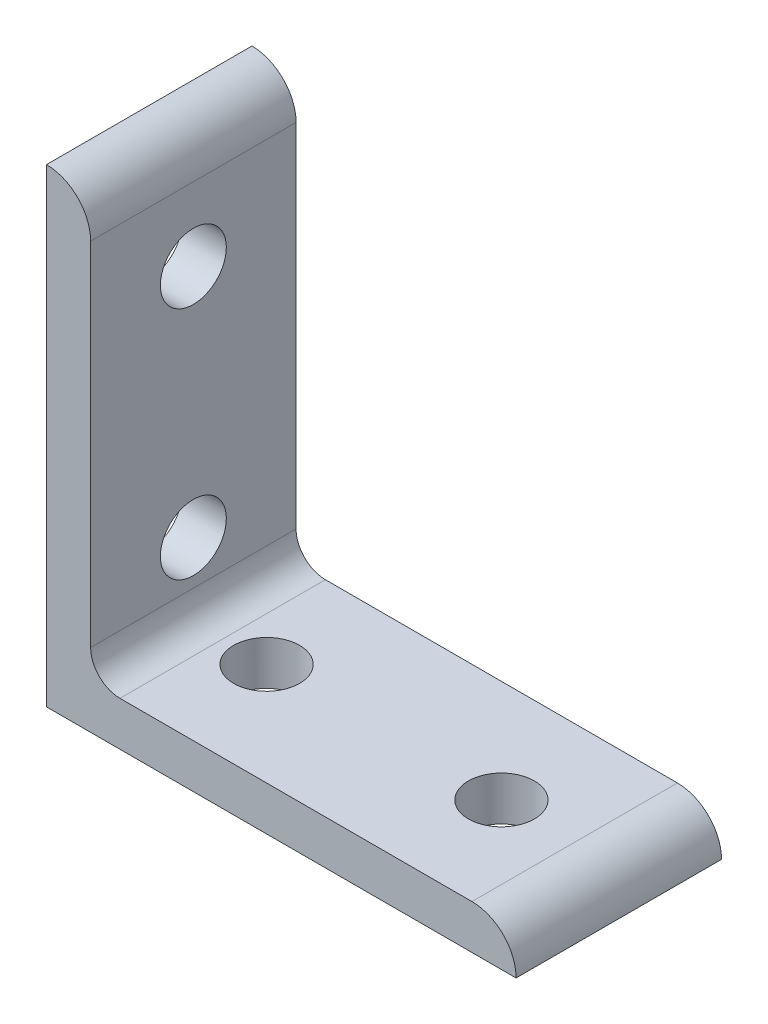
SolidWorks part; units mm, degrees
ref_plane "Front Plane" through (0, 0, 0) normal (0, 0, 1) x (1, 0, 0)
ref_plane "Top Plane" through (0, 0, 0) normal (0, 1, 0) x (1, 0, 0)
ref_plane "Right Plane" through (0, 0, 0) normal (1, 0, 0) x (0, 0, -1)
sketch "Sketch1" plane through (0, 0, 0) normal (0, 0, 1) x (1, 0, 0)
  line L0 (0, 0) -> (0, 50.8)
  line L1 (4.7752, 46.0248) -> (4.7752, 50.8) construction
  line L2 (4.7752, 46.0248) -> (4.7752, 7.9502)
  line L3 (7.9502, 4.7752) -> (46.0248, 4.7752)
  line L4 (4.7752, 50.8) -> (0, 50.8) construction
  line L5 (50.8, 0) -> (0, 0)
  line L6 (46.0248, 4.7752) -> (50.8, 4.7752) construction
  line L7 (50.8, 4.7752) -> (50.8, 0) construction
  arc A0 (4.7752, 46.0248) -> (0, 50.8) centre (0, 46.0248) ccw
  arc A1 (50.8, 0) -> (46.0248, 4.7752) centre (46.0248, 0) ccw
  arc A2 (4.7752, 7.9502) -> (7.9502, 4.7752) centre (7.9502, 7.9502) ccw
  point P10 (4.7752, 48.4124)
  dimension "E" = 3.175
  dimension "D" = 4.7752
  dimension "C" = 50.8
  dimension "B" = 50.8
extrude "Boss-Extrude1" add sketch "Sketch1" along normal mid plane 22.225
sketch "Sketch2" plane through (0, 0, 0) normal (0, 1, 0) x (1, 0, 0)
  line L0 (0, 0) -> (12.7, 0) construction
  line L1 (12.7, 0) -> (38.1, 0) construction
  circle A0 centre (12.7, 0) radius 3.5687
  circle A1 centre (38.1, 0) radius 3.5687
extrude "Cut-Extrude1" cut sketch "Sketch2" along normal through all
sketch "Sketch3" plane through (0, 0, 0) normal (1, 0, 0) x (0, 0, -1)
  line L0 (0, 0) -> (0, 12.7) construction
  line L1 (0, 12.7) -> (0, 38.1) construction
  circle A0 centre (0, 12.7) radius 3.5687
  circle A1 centre (0, 38.1) radius 3.5687
  dimension "D1" = 12.7
  dimension "D2" = 25.4
extrude "Cut-Extrude2" cut sketch "Sketch3" along normal through all
equation "\"E@Sketch3\" = \"E@Sketch2\""
equation "\"D1@Sketch3\" = \"D1@Sketch2\""
equation "\"D2@Sketch3\" = \"D2@Sketch2\""
